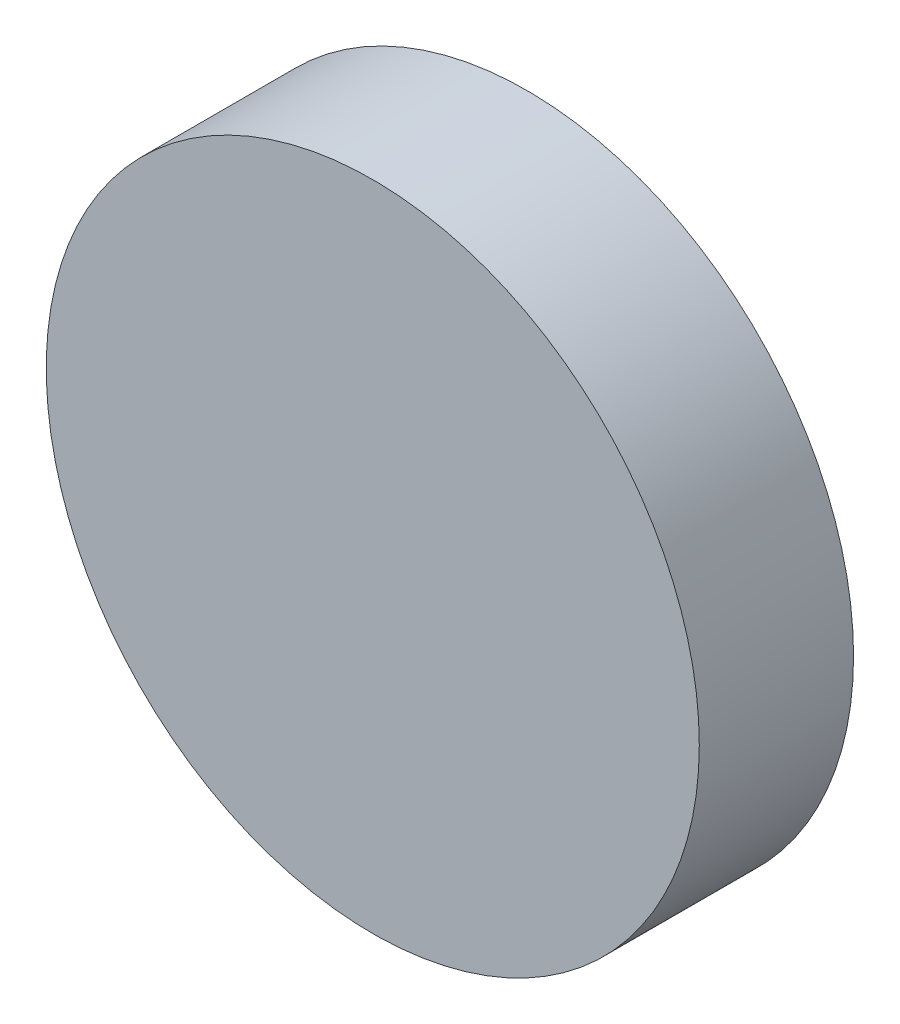
SolidWorks part; units mm, degrees
ref_plane "前视基准面" through (0, 0, 0) normal (0, 0, 1) x (1, 0, 0)
ref_plane "上视基准面" through (0, 0, 0) normal (0, 1, 0) x (1, 0, 0)
ref_plane "右视基准面" through (0, 0, 0) normal (1, 0, 0) x (0, 0, -1)
sketch "草图1" plane through (0, 0, 0) normal (0, 0, 1) x (1, 0, 0)
  circle A0 centre (0, 0) radius 6.35
  dimension "D1" = 12.7
extrude "凸台-拉伸1" add sketch "草图1" along normal blind 3
